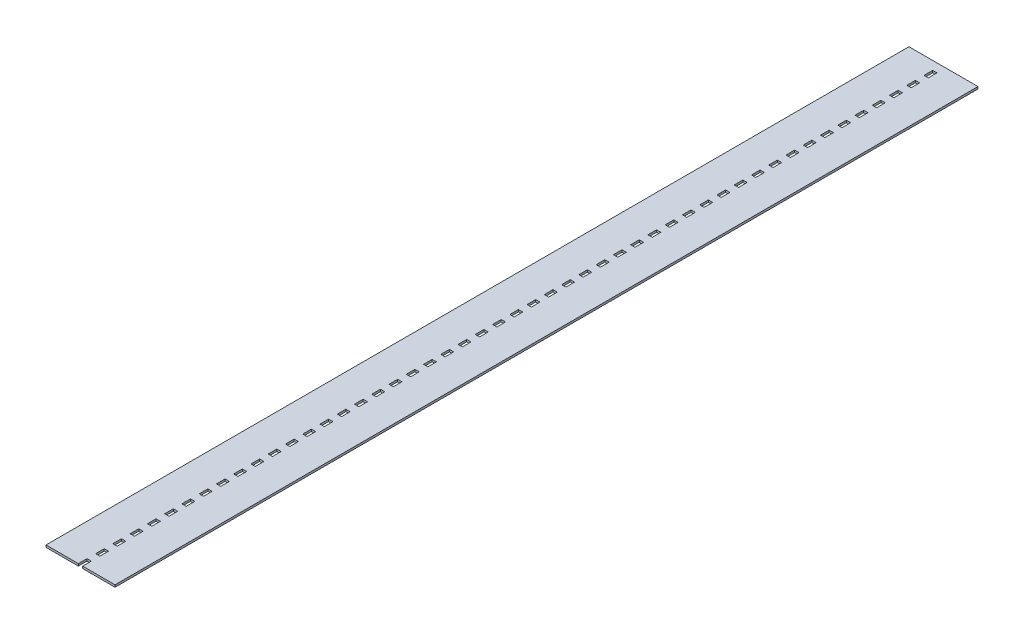
SolidWorks part; units mm, degrees
material "Gray Cast Iron"
ref_plane "Front Plane" through (0, 0, 0) normal (0, 0, 1) x (1, 0, 0)
ref_plane "Top Plane" through (0, 0, 0) normal (0, 1, 0) x (1, 0, 0)
ref_plane "Right Plane" through (0, 0, 0) normal (1, 0, 0) x (0, 0, -1)
sketch "Sketch1" plane through (0, 0, 0) normal (0, 1, 0) x (1, 0, 0)
  line L0 (-65.5547, -62.3983) -> (-65.5547, 37.6017) construction
  line L1 (-465.5547, 9937.6017) -> (334.4453, 9937.6017)
  line L2 (-465.5547, 9937.6017) -> (-465.5547, -62.3983)
  line L4 (334.4453, 9937.6017) -> (334.4453, -62.3983)
  line L5 (-90.5547, 37.6017) -> (-40.5547, 37.6017)
  line L6 (-90.5547, 37.6017) -> (-90.5547, -62.3983)
  line L7 (-40.5547, 37.6017) -> (-40.5547, -62.3983)
  line L8 (-465.5547, -62.3983) -> (-40.5547, -62.3983)
  line L9 (-90.5547, -62.3983) -> (334.4453, -62.3983)
  line L10 (-90.5547, -62.3983) -> (-40.5547, -62.3983)
  line L11 (-90.5547, 237.6017) -> (-40.5547, 237.6017)
  line L12 (-90.5547, 237.6017) -> (-90.5547, 137.6017)
  line L13 (-40.5547, 237.6017) -> (-40.5547, 137.6017)
  line L14 (-90.5547, 137.6017) -> (-40.5547, 137.6017)
  line L15 (-90.5547, 437.6017) -> (-40.5547, 437.6017)
  line L16 (-90.5547, 437.6017) -> (-90.5547, 337.6017)
  line L17 (-40.5547, 437.6017) -> (-40.5547, 337.6017)
  line L18 (-90.5547, 337.6017) -> (-40.5547, 337.6017)
  line L19 (-90.5547, 637.6017) -> (-40.5547, 637.6017)
  line L20 (-90.5547, 637.6017) -> (-90.5547, 537.6017)
  line L21 (-40.5547, 637.6017) -> (-40.5547, 537.6017)
  line L22 (-90.5547, 537.6017) -> (-40.5547, 537.6017)
  line L23 (-90.5547, 837.6017) -> (-40.5547, 837.6017)
  line L24 (-90.5547, 837.6017) -> (-90.5547, 737.6017)
  line L25 (-40.5547, 837.6017) -> (-40.5547, 737.6017)
  line L26 (-90.5547, 737.6017) -> (-40.5547, 737.6017)
  line L27 (-90.5547, 1037.6017) -> (-40.5547, 1037.6017)
  line L28 (-90.5547, 1037.6017) -> (-90.5547, 937.6017)
  line L29 (-40.5547, 1037.6017) -> (-40.5547, 937.6017)
  line L30 (-90.5547, 937.6017) -> (-40.5547, 937.6017)
  line L31 (-90.5547, 1237.6017) -> (-40.5547, 1237.6017)
  line L32 (-90.5547, 1237.6017) -> (-90.5547, 1137.6017)
  line L33 (-40.5547, 1237.6017) -> (-40.5547, 1137.6017)
  line L34 (-90.5547, 1137.6017) -> (-40.5547, 1137.6017)
  line L35 (-90.5547, 1437.6017) -> (-40.5547, 1437.6017)
  line L36 (-90.5547, 1437.6017) -> (-90.5547, 1337.6017)
  line L37 (-40.5547, 1437.6017) -> (-40.5547, 1337.6017)
  line L38 (-90.5547, 1337.6017) -> (-40.5547, 1337.6017)
  line L39 (-90.5547, 1637.6017) -> (-40.5547, 1637.6017)
  line L40 (-90.5547, 1637.6017) -> (-90.5547, 1537.6017)
  line L41 (-40.5547, 1637.6017) -> (-40.5547, 1537.6017)
  line L42 (-90.5547, 1537.6017) -> (-40.5547, 1537.6017)
  line L43 (-90.5547, 1837.6017) -> (-40.5547, 1837.6017)
  line L44 (-90.5547, 1837.6017) -> (-90.5547, 1737.6017)
  line L45 (-40.5547, 1837.6017) -> (-40.5547, 1737.6017)
  line L46 (-90.5547, 1737.6017) -> (-40.5547, 1737.6017)
  line L47 (-90.5547, 2037.6017) -> (-40.5547, 2037.6017)
  line L48 (-90.5547, 2037.6017) -> (-90.5547, 1937.6017)
  line L49 (-40.5547, 2037.6017) -> (-40.5547, 1937.6017)
  line L50 (-90.5547, 1937.6017) -> (-40.5547, 1937.6017)
  line L51 (-90.5547, 2237.6017) -> (-40.5547, 2237.6017)
  line L52 (-90.5547, 2237.6017) -> (-90.5547, 2137.6017)
  line L53 (-40.5547, 2237.6017) -> (-40.5547, 2137.6017)
  line L54 (-90.5547, 2137.6017) -> (-40.5547, 2137.6017)
  line L55 (-90.5547, 2437.6017) -> (-40.5547, 2437.6017)
  line L56 (-90.5547, 2437.6017) -> (-90.5547, 2337.6017)
  line L57 (-40.5547, 2437.6017) -> (-40.5547, 2337.6017)
  line L58 (-90.5547, 2337.6017) -> (-40.5547, 2337.6017)
  line L59 (-90.5547, 2637.6017) -> (-40.5547, 2637.6017)
  line L60 (-90.5547, 2637.6017) -> (-90.5547, 2537.6017)
  line L61 (-40.5547, 2637.6017) -> (-40.5547, 2537.6017)
  line L62 (-90.5547, 2537.6017) -> (-40.5547, 2537.6017)
  line L63 (-90.5547, 2837.6017) -> (-40.5547, 2837.6017)
  line L64 (-90.5547, 2837.6017) -> (-90.5547, 2737.6017)
  line L65 (-40.5547, 2837.6017) -> (-40.5547, 2737.6017)
  line L66 (-90.5547, 2737.6017) -> (-40.5547, 2737.6017)
  line L67 (-90.5547, 3037.6017) -> (-40.5547, 3037.6017)
  line L68 (-90.5547, 3037.6017) -> (-90.5547, 2937.6017)
  line L69 (-40.5547, 3037.6017) -> (-40.5547, 2937.6017)
  line L70 (-90.5547, 2937.6017) -> (-40.5547, 2937.6017)
  line L71 (-90.5547, 3237.6017) -> (-40.5547, 3237.6017)
  line L72 (-90.5547, 3237.6017) -> (-90.5547, 3137.6017)
  line L73 (-40.5547, 3237.6017) -> (-40.5547, 3137.6017)
  line L74 (-90.5547, 3137.6017) -> (-40.5547, 3137.6017)
  line L75 (-90.5547, 3437.6017) -> (-40.5547, 3437.6017)
  line L76 (-90.5547, 3437.6017) -> (-90.5547, 3337.6017)
  line L77 (-40.5547, 3437.6017) -> (-40.5547, 3337.6017)
  line L78 (-90.5547, 3337.6017) -> (-40.5547, 3337.6017)
  line L79 (-90.5547, 3637.6017) -> (-40.5547, 3637.6017)
  line L80 (-90.5547, 3637.6017) -> (-90.5547, 3537.6017)
  line L81 (-40.5547, 3637.6017) -> (-40.5547, 3537.6017)
  line L82 (-90.5547, 3537.6017) -> (-40.5547, 3537.6017)
  line L83 (-90.5547, 3837.6017) -> (-40.5547, 3837.6017)
  line L84 (-90.5547, 3837.6017) -> (-90.5547, 3737.6017)
  line L85 (-40.5547, 3837.6017) -> (-40.5547, 3737.6017)
  line L86 (-90.5547, 3737.6017) -> (-40.5547, 3737.6017)
  line L87 (-90.5547, 4037.6017) -> (-40.5547, 4037.6017)
  line L88 (-90.5547, 4037.6017) -> (-90.5547, 3937.6017)
  line L89 (-40.5547, 4037.6017) -> (-40.5547, 3937.6017)
  line L90 (-90.5547, 3937.6017) -> (-40.5547, 3937.6017)
  line L91 (-90.5547, 4237.6017) -> (-40.5547, 4237.6017)
  line L92 (-90.5547, 4237.6017) -> (-90.5547, 4137.6017)
  line L93 (-40.5547, 4237.6017) -> (-40.5547, 4137.6017)
  line L94 (-90.5547, 4137.6017) -> (-40.5547, 4137.6017)
  line L95 (-90.5547, 4437.6017) -> (-40.5547, 4437.6017)
  line L96 (-90.5547, 4437.6017) -> (-90.5547, 4337.6017)
  line L97 (-40.5547, 4437.6017) -> (-40.5547, 4337.6017)
  line L98 (-90.5547, 4337.6017) -> (-40.5547, 4337.6017)
  line L99 (-90.5547, 4637.6017) -> (-40.5547, 4637.6017)
  line L100 (-90.5547, 4637.6017) -> (-90.5547, 4537.6017)
  line L101 (-40.5547, 4637.6017) -> (-40.5547, 4537.6017)
  line L102 (-90.5547, 4537.6017) -> (-40.5547, 4537.6017)
  line L103 (-90.5547, 4837.6017) -> (-40.5547, 4837.6017)
  line L104 (-90.5547, 4837.6017) -> (-90.5547, 4737.6017)
  line L105 (-40.5547, 4837.6017) -> (-40.5547, 4737.6017)
  line L106 (-90.5547, 4737.6017) -> (-40.5547, 4737.6017)
  line L107 (-90.5547, 5037.6017) -> (-40.5547, 5037.6017)
  line L108 (-90.5547, 5037.6017) -> (-90.5547, 4937.6017)
  line L109 (-40.5547, 5037.6017) -> (-40.5547, 4937.6017)
  line L110 (-90.5547, 4937.6017) -> (-40.5547, 4937.6017)
  line L111 (-90.5547, 5237.6017) -> (-40.5547, 5237.6017)
  line L112 (-90.5547, 5237.6017) -> (-90.5547, 5137.6017)
  line L113 (-40.5547, 5237.6017) -> (-40.5547, 5137.6017)
  line L114 (-90.5547, 5137.6017) -> (-40.5547, 5137.6017)
  line L115 (-90.5547, 5437.6017) -> (-40.5547, 5437.6017)
  line L116 (-90.5547, 5437.6017) -> (-90.5547, 5337.6017)
  line L117 (-40.5547, 5437.6017) -> (-40.5547, 5337.6017)
  line L118 (-90.5547, 5337.6017) -> (-40.5547, 5337.6017)
  line L119 (-90.5547, 5637.6017) -> (-40.5547, 5637.6017)
  line L120 (-90.5547, 5637.6017) -> (-90.5547, 5537.6017)
  line L121 (-40.5547, 5637.6017) -> (-40.5547, 5537.6017)
  line L122 (-90.5547, 5537.6017) -> (-40.5547, 5537.6017)
  line L123 (-90.5547, 5837.6017) -> (-40.5547, 5837.6017)
  line L124 (-90.5547, 5837.6017) -> (-90.5547, 5737.6017)
  line L125 (-40.5547, 5837.6017) -> (-40.5547, 5737.6017)
  line L126 (-90.5547, 5737.6017) -> (-40.5547, 5737.6017)
  line L127 (-90.5547, 6037.6017) -> (-40.5547, 6037.6017)
  line L128 (-90.5547, 6037.6017) -> (-90.5547, 5937.6017)
  line L129 (-40.5547, 6037.6017) -> (-40.5547, 5937.6017)
  line L130 (-90.5547, 5937.6017) -> (-40.5547, 5937.6017)
  line L131 (-90.5547, 6237.6017) -> (-40.5547, 6237.6017)
  line L132 (-90.5547, 6237.6017) -> (-90.5547, 6137.6017)
  line L133 (-40.5547, 6237.6017) -> (-40.5547, 6137.6017)
  line L134 (-90.5547, 6137.6017) -> (-40.5547, 6137.6017)
  line L135 (-90.5547, 6437.6017) -> (-40.5547, 6437.6017)
  line L136 (-90.5547, 6437.6017) -> (-90.5547, 6337.6017)
  line L137 (-40.5547, 6437.6017) -> (-40.5547, 6337.6017)
  line L138 (-90.5547, 6337.6017) -> (-40.5547, 6337.6017)
  line L139 (-90.5547, 6637.6017) -> (-40.5547, 6637.6017)
  line L140 (-90.5547, 6637.6017) -> (-90.5547, 6537.6017)
  line L141 (-40.5547, 6637.6017) -> (-40.5547, 6537.6017)
  line L142 (-90.5547, 6537.6017) -> (-40.5547, 6537.6017)
  line L143 (-90.5547, 6837.6017) -> (-40.5547, 6837.6017)
  line L144 (-90.5547, 6837.6017) -> (-90.5547, 6737.6017)
  line L145 (-40.5547, 6837.6017) -> (-40.5547, 6737.6017)
  line L146 (-90.5547, 6737.6017) -> (-40.5547, 6737.6017)
  line L147 (-90.5547, 7037.6017) -> (-40.5547, 7037.6017)
  line L148 (-90.5547, 7037.6017) -> (-90.5547, 6937.6017)
  line L149 (-40.5547, 7037.6017) -> (-40.5547, 6937.6017)
  line L150 (-90.5547, 6937.6017) -> (-40.5547, 6937.6017)
  line L151 (-90.5547, 7237.6017) -> (-40.5547, 7237.6017)
  line L152 (-90.5547, 7237.6017) -> (-90.5547, 7137.6017)
  line L153 (-40.5547, 7237.6017) -> (-40.5547, 7137.6017)
  line L154 (-90.5547, 7137.6017) -> (-40.5547, 7137.6017)
  line L155 (-90.5547, 7437.6017) -> (-40.5547, 7437.6017)
  line L156 (-90.5547, 7437.6017) -> (-90.5547, 7337.6017)
  line L157 (-40.5547, 7437.6017) -> (-40.5547, 7337.6017)
  line L158 (-90.5547, 7337.6017) -> (-40.5547, 7337.6017)
  line L159 (-90.5547, 7637.6017) -> (-40.5547, 7637.6017)
  line L160 (-90.5547, 7637.6017) -> (-90.5547, 7537.6017)
  line L161 (-40.5547, 7637.6017) -> (-40.5547, 7537.6017)
  line L162 (-90.5547, 7537.6017) -> (-40.5547, 7537.6017)
  line L163 (-90.5547, 7837.6017) -> (-40.5547, 7837.6017)
  line L164 (-90.5547, 7837.6017) -> (-90.5547, 7737.6017)
  line L165 (-40.5547, 7837.6017) -> (-40.5547, 7737.6017)
  line L166 (-90.5547, 7737.6017) -> (-40.5547, 7737.6017)
  line L167 (-90.5547, 8037.6017) -> (-40.5547, 8037.6017)
  line L168 (-90.5547, 8037.6017) -> (-90.5547, 7937.6017)
  line L169 (-40.5547, 8037.6017) -> (-40.5547, 7937.6017)
  line L170 (-90.5547, 7937.6017) -> (-40.5547, 7937.6017)
  line L171 (-90.5547, 8237.6017) -> (-40.5547, 8237.6017)
  line L172 (-90.5547, 8237.6017) -> (-90.5547, 8137.6017)
  line L173 (-40.5547, 8237.6017) -> (-40.5547, 8137.6017)
  line L174 (-90.5547, 8137.6017) -> (-40.5547, 8137.6017)
  line L175 (-90.5547, 8437.6017) -> (-40.5547, 8437.6017)
  line L176 (-90.5547, 8437.6017) -> (-90.5547, 8337.6017)
  line L177 (-40.5547, 8437.6017) -> (-40.5547, 8337.6017)
  line L178 (-90.5547, 8337.6017) -> (-40.5547, 8337.6017)
  line L179 (-90.5547, 8637.6017) -> (-40.5547, 8637.6017)
  line L180 (-90.5547, 8637.6017) -> (-90.5547, 8537.6017)
  line L181 (-40.5547, 8637.6017) -> (-40.5547, 8537.6017)
  line L182 (-90.5547, 8537.6017) -> (-40.5547, 8537.6017)
  line L183 (-90.5547, 8837.6017) -> (-40.5547, 8837.6017)
  line L184 (-90.5547, 8837.6017) -> (-90.5547, 8737.6017)
  line L185 (-40.5547, 8837.6017) -> (-40.5547, 8737.6017)
  line L186 (-90.5547, 8737.6017) -> (-40.5547, 8737.6017)
  line L187 (-90.5547, 9037.6017) -> (-40.5547, 9037.6017)
  line L188 (-90.5547, 9037.6017) -> (-90.5547, 8937.6017)
  line L189 (-40.5547, 9037.6017) -> (-40.5547, 8937.6017)
  line L190 (-90.5547, 8937.6017) -> (-40.5547, 8937.6017)
  line L191 (-90.5547, 9237.6017) -> (-40.5547, 9237.6017)
  line L192 (-90.5547, 9237.6017) -> (-90.5547, 9137.6017)
  line L193 (-40.5547, 9237.6017) -> (-40.5547, 9137.6017)
  line L194 (-90.5547, 9137.6017) -> (-40.5547, 9137.6017)
  line L195 (-90.5547, 9437.6017) -> (-40.5547, 9437.6017)
  line L196 (-90.5547, 9437.6017) -> (-90.5547, 9337.6017)
  line L197 (-40.5547, 9437.6017) -> (-40.5547, 9337.6017)
  line L198 (-90.5547, 9337.6017) -> (-40.5547, 9337.6017)
  line L199 (-90.5547, 9637.6017) -> (-40.5547, 9637.6017)
  line L200 (-90.5547, 9637.6017) -> (-90.5547, 9537.6017)
  line L201 (-40.5547, 9637.6017) -> (-40.5547, 9537.6017)
  line L202 (-90.5547, 9537.6017) -> (-40.5547, 9537.6017)
  line L203 (-90.5547, 9837.6017) -> (-40.5547, 9837.6017)
  line L204 (-90.5547, 9837.6017) -> (-90.5547, 9737.6017)
  line L205 (-40.5547, 9837.6017) -> (-40.5547, 9737.6017)
  line L206 (-90.5547, 9737.6017) -> (-40.5547, 9737.6017)
  line L207 (-90.5547, 10037.6017) -> (-40.5547, 10037.6017)
  line L208 (-90.5547, 10037.6017) -> (-90.5547, 9937.6017)
  line L209 (-40.5547, 10037.6017) -> (-40.5547, 9937.6017)
  line L210 (-90.5547, 9937.6017) -> (-40.5547, 9937.6017)
  dimension "D1" = 800
  dimension "D2" = 51
  dimension "D3" = 10000
  dimension "D4" = 375
  dimension "D5" = 50
  dimension "D6" = 100
extrude "Boss-Extrude1" add sketch "Sketch1" along normal blind 25 contours L6 L9 L4 L1 L2 L8 L7 L5 L12 L14 L13 L11 L16 L18 L17 L15 L20 L22 L21 L19 L24 L26 L25 L23 L28 L30 L29 L27 L32 L34 L33 L31 L36 L38 L37 L35 L40 L42 L41 L39
sketch "Sketch2" plane through (0, 25, 0) normal (0, 1, 0) x (1, 0, 0)
  line L0 (-465.5547, 9937.6017) -> (334.4453, 9937.6017) construction
  line L1 (-465.5547, 9937.6017) -> (-465.5547, -62.3983) construction
  line L4 (-90.5547, 9737.6017) -> (-40.5547, 9737.6017) construction
  point P3 (-65.5547, 9937.6017)
  point P8 (-65.5547, -62.3983)
  dimension "D1" = 400
  dimension "D2" = 9800
